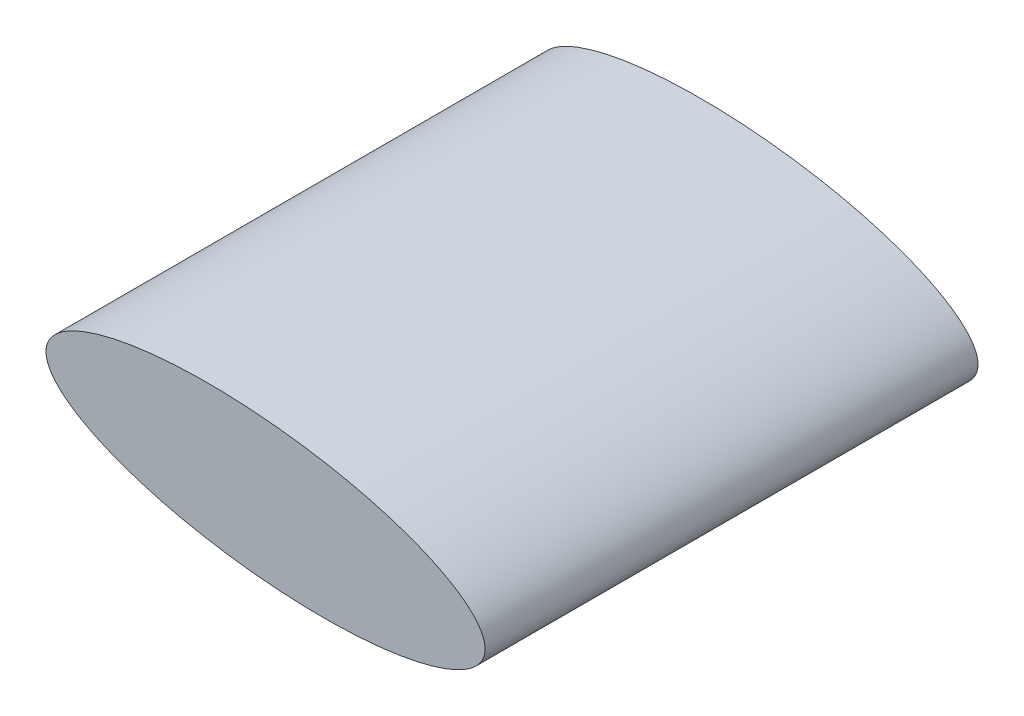
SolidWorks part; units mm, degrees
ref_plane "Alzado" through (0, 0, 0) normal (0, 0, 1) x (1, 0, 0)
ref_plane "Planta" through (0, 0, 0) normal (0, 1, 0) x (1, 0, 0)
ref_plane "Vista lateral" through (0, 0, 0) normal (1, 0, 0) x (0, 0, -1)
ref_plane "Plane1" through (0, 0, -1.175) normal (0, 0, -1) x (-1, 0, 0)
sketch "Sketch1" plane through (0, 0, -1.175) normal (0, 0, -1) x (-1, 0, 0)
  ellipse E0 centre (0, 0) end of major axis (-0.2449, -0.0237) minor radius 0.078
extrude "Boss-Extrude1" add sketch "Sketch1" against normal blind 0.55
